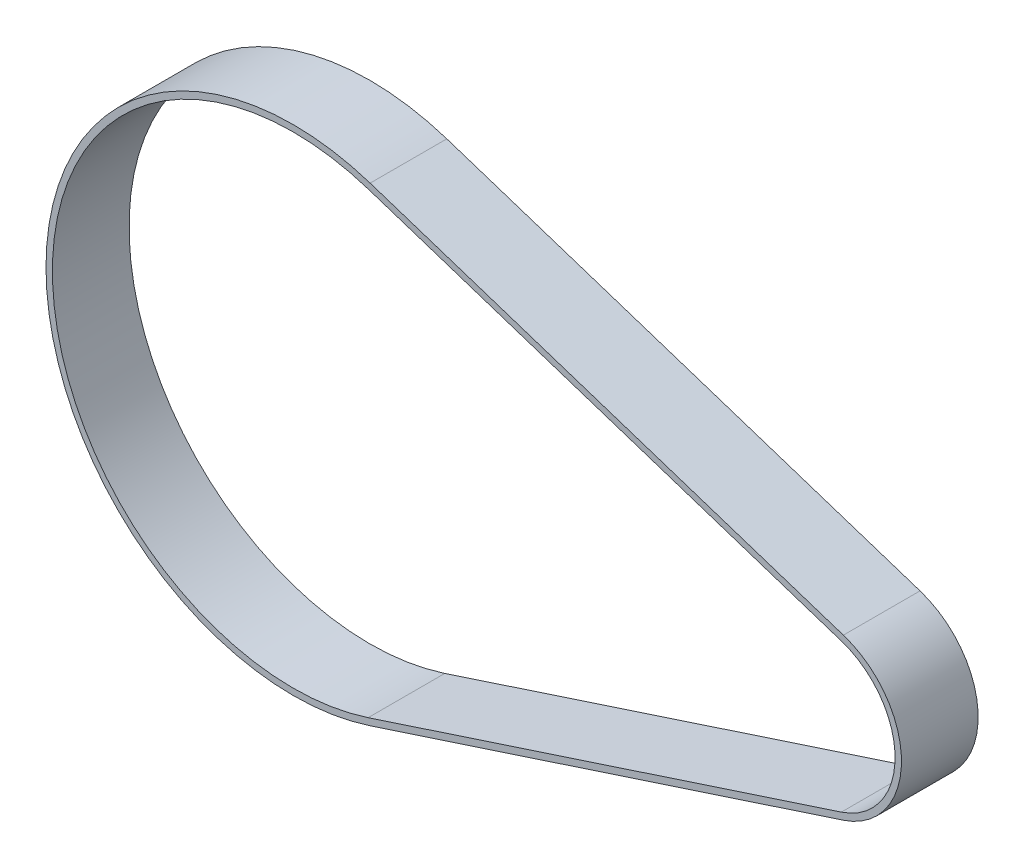
SolidWorks part; units mm, degrees
material "Caucho"
ref_plane "Alzado" through (0, 0, 0) normal (0, 0, 1) x (1, 0, 0)
ref_plane "Planta" through (0, 0, 0) normal (0, 1, 0) x (1, 0, 0)
ref_plane "Vista lateral" through (0, 0, 0) normal (1, 0, 0) x (0, 0, -1)
sketch "Croquis1" plane through (0, 0, 0) normal (0, 0, 1) x (1, 0, 0)
  line L0 (5.8619, 17.9154) -> (42.897, 5.7975)
  line L1 (0, 0) -> (79.1587, 0) construction
  line L2 (42.897, -5.7975) -> (5.8619, -17.9154)
  line L3 (43.0524, -6.2728) -> (6.0174, -18.3906)
  line L4 (6.0174, 18.3906) -> (43.0524, 6.2728)
  arc A0 (5.8619, 17.9154) -> (5.8619, -17.9154) centre (0, 0) ccw
  arc A1 (42.897, -5.7975) -> (42.897, 5.7975) centre (41, 0) ccw
  arc A2 (6.0174, 18.3906) -> (6.0174, -18.3906) centre (0, 0) ccw
  arc A3 (43.0524, -6.2728) -> (43.0524, 6.2728) centre (41, 0) ccw
  dimension "D1" = 12.2
  dimension "D2" = 37.7
  dimension "D3" = 41
  dimension "D4" = 0.5
extrude "Saliente-Extruir1" add sketch "Croquis1" along normal blind 6
